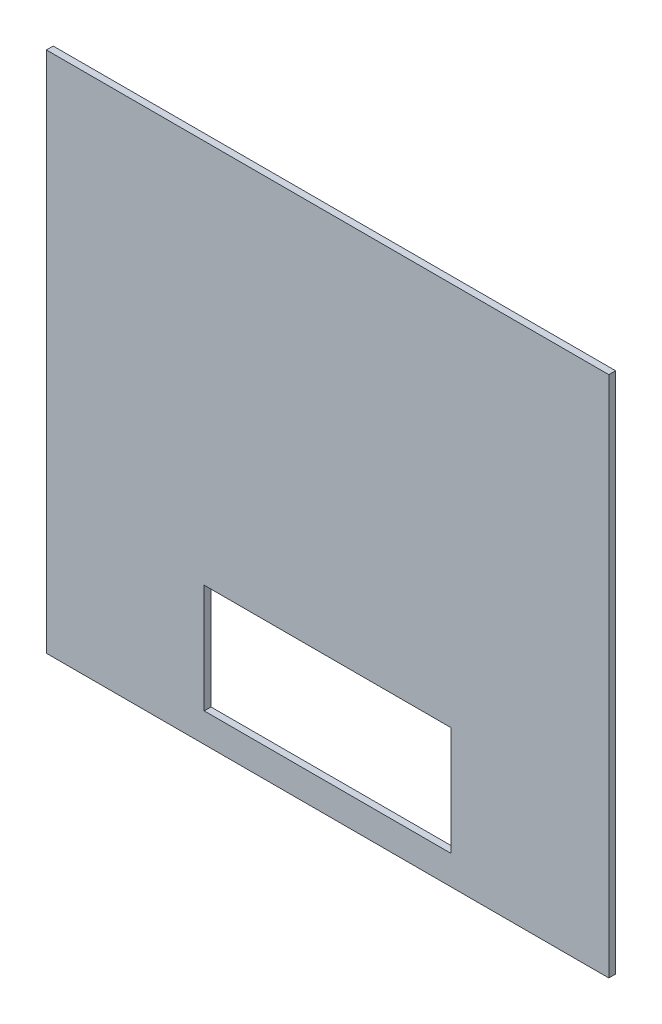
SolidWorks part; units mm, degrees
ref_plane "Front Plane" through (0, 0, 0) normal (0, 0, 1) x (1, 0, 0)
ref_plane "Top Plane" through (0, 0, 0) normal (0, 1, 0) x (1, 0, 0)
ref_plane "Right Plane" through (0, 0, 0) normal (1, 0, 0) x (0, 0, -1)
sketch "Sketch1" plane through (0, 0, 0) normal (0, 0, 1) x (1, 0, 0)
  line L1 (-492.125, -457.2) -> (492.125, -457.2)
  line L2 (-492.125, -457.2) -> (-492.125, 457.2)
  line L3 (-492.125, 457.2) -> (492.125, 457.2)
  line L4 (492.125, -457.2) -> (492.125, 457.2)
  line L5 (-492.125, -457.2) -> (492.125, 457.2) construction
  line L6 (-492.125, 457.2) -> (492.125, -457.2) construction
  point P0 (0, 0)
  dimension "D1" = 914.4
  dimension "D2" = 984.25
extrude "Boss-Extrude1" add sketch "Sketch1" along normal blind 11.9062
sketch "Sketch3" plane through (0, 0, 11.9062) normal (0, 0, 1) x (1, 0, 0)
  line L0 (0, -457.2) -> (0, -406.4) construction
  line L1 (-492.125, -457.2) -> (492.125, -457.2) construction
  line L2 (0, -406.4) -> (215.9, -406.4)
  line L3 (215.9, -406.4) -> (215.9, -215.9)
  line L4 (215.9, -215.9) -> (-215.9, -215.9)
  line L5 (-215.9, -215.9) -> (-215.9, -406.4)
  line L6 (-215.9, -406.4) -> (0, -406.4)
  dimension "D1" = 50.8
  dimension "D2" = 215.9
  dimension "D3" = 431.8
  dimension "D4" = 190.5
extrude "Cut-Extrude1" cut sketch "Sketch3" against normal through all both and the other way through all
